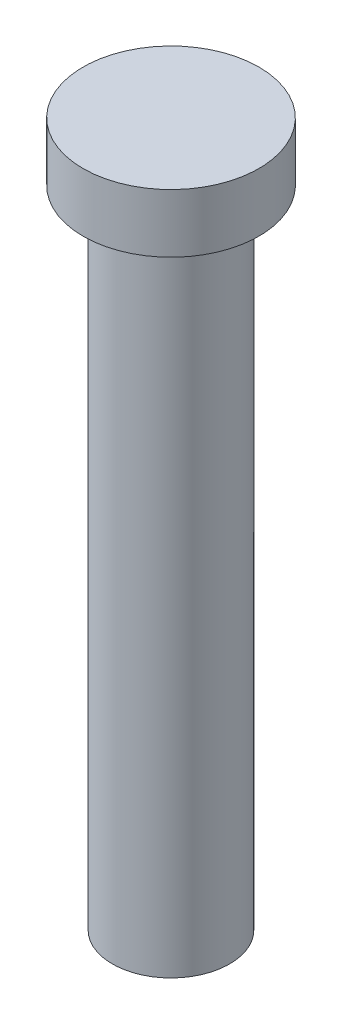
SolidWorks part; units mm, degrees
ref_plane "Front Plane" through (0, 0, 0) normal (0, 0, 1) x (1, 0, 0)
ref_plane "Top Plane" through (0, 0, 0) normal (0, 1, 0) x (1, 0, 0)
ref_plane "Right Plane" through (0, 0, 0) normal (1, 0, 0) x (0, 0, -1)
sketch "Sketch1" plane through (0, 0, 0) normal (0, 1, 0) x (1, 0, 0)
  circle A0 centre (0, 0) radius 15
  dimension "D1" = 30
extrude "Boss-Extrude1" add sketch "Sketch1" along normal blind 10
sketch "Sketch2" plane through (0, 0, 0) normal (0, -1, 0) x (1, 0, 0)
  circle A0 centre (0, 0) radius 10
  dimension "D1" = 20
extrude "Boss-Extrude2" add sketch "Sketch2" along normal blind 110
